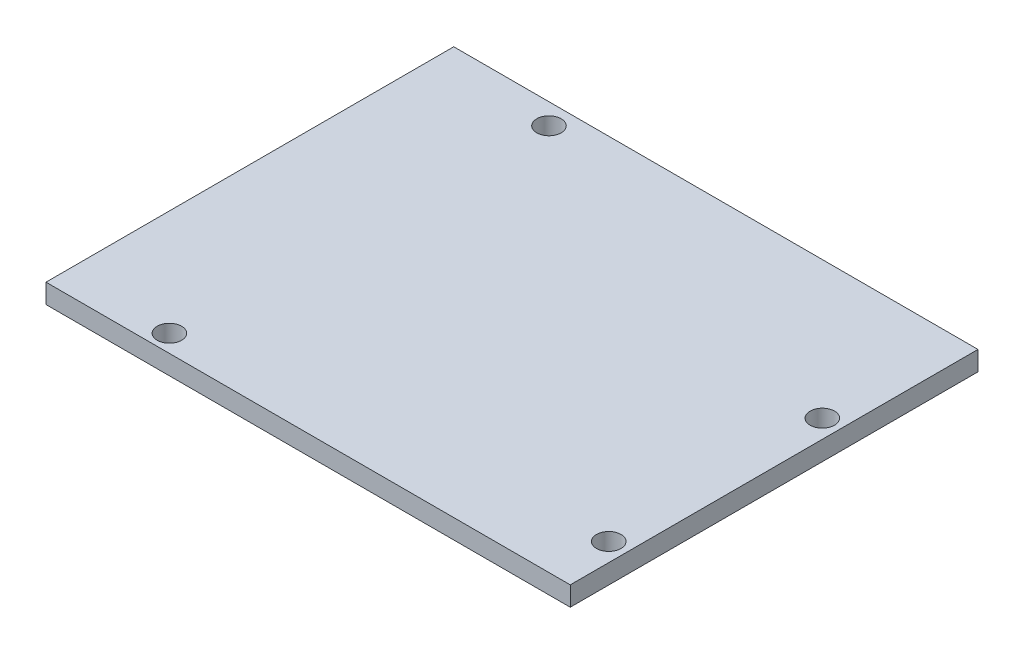
SolidWorks part; units mm, degrees
ref_plane "Front Plane" through (0, 0, 0) normal (0, 0, 1) x (1, 0, 0)
ref_plane "Top Plane" through (0, 0, 0) normal (0, 1, 0) x (1, 0, 0)
ref_plane "Right Plane" through (0, 0, 0) normal (1, 0, 0) x (0, 0, -1)
sketch "Sketch1" plane through (0, 0, 0) normal (0, 1, 0) x (1, 0, 0)
  line L1 (-36.0597, 25.7204) -> (32.5203, 25.7204)
  line L2 (-36.0597, 25.7204) -> (-36.0597, -27.6196)
  line L3 (-36.0597, -27.6196) -> (32.5203, -27.6196)
  line L4 (32.5203, 25.7204) -> (32.5203, -27.6196)
  dimension "D1" = 53.34
  dimension "D2" = 68.58
extrude "Boss-Extrude1" add sketch "Sketch1" along normal blind 2.54
hole_wizard "M3 Clearance Hole1" positions "Sketch3" profile "Sketch2" hole size "M3" standard "Ansi Metric"
sketch "Sketch3" plane through (0, 2.54, 0) normal (0, 1, 0) x (-1, 0, 0)
  point P0 (-30.1253, -7.7524)
  point P1 (-30.1253, 20.1876)
  point P4 (22.1987, 25.3354)
  point P7 (20.8747, -22.9924)
  dimension "D1" = 27.94
  dimension "D4" = 52.324
  dimension "D5" = 5.1477
  dimension "D6" = 51
  dimension "D7" = 15.24
  dimension "D8" = 48.3277
sketch "Sketch2" plane through (30.1253, 2.54, -7.7524) normal (1, 0, 0) x (0, 0, 1)
  line L0 (0, 0) -> (0, 6.0414)
  line L1 (0, 6.0414) -> (1.6, 5.08)
  line L2 (1.6, 5.08) -> (1.6, 0)
  line L5 (1.6, 0) -> (0, 0)
  line L10 (0, 6.0414) -> (-1.6, 5.08) construction
  line L11 (0, -6.35) -> (0, 107.95) construction
  dimension "Hole Dia." = 3.2
  dimension "Hole Depth" = 5.08
  dimension "Drill Angle" = 118
